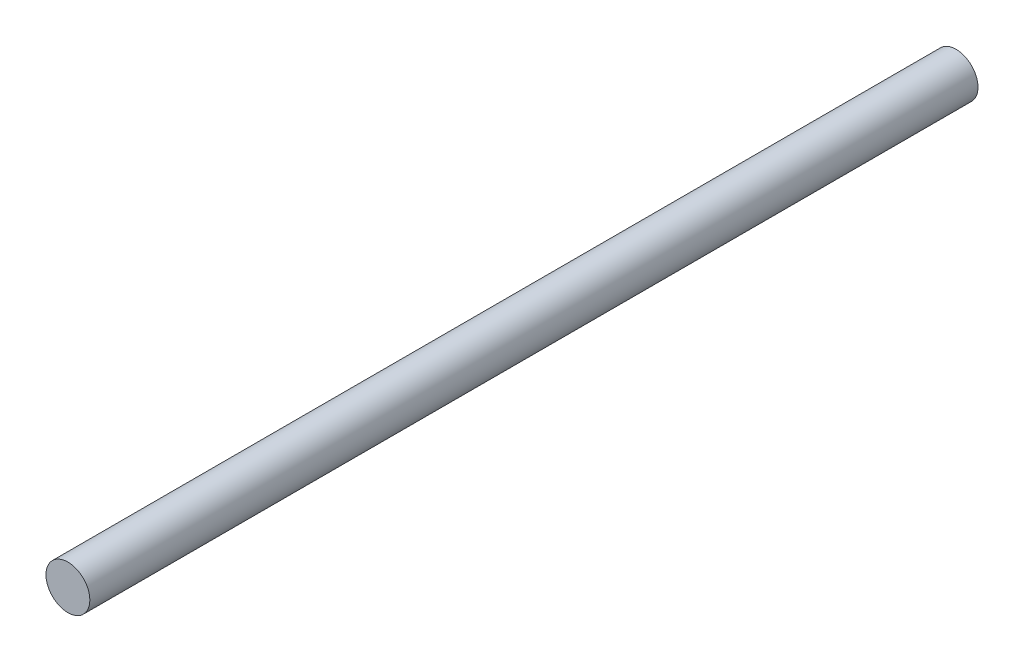
SolidWorks part; units mm, degrees
ref_plane "Front Plane" through (0, 0, 0) normal (0, 0, 1) x (1, 0, 0)
ref_plane "Top Plane" through (0, 0, 0) normal (0, 1, 0) x (1, 0, 0)
ref_plane "Right Plane" through (0, 0, 0) normal (1, 0, 0) x (0, 0, -1)
sketch "Sketch1" plane through (0, 0, 0) normal (0, 0, 1) x (1, 0, 0)
  circle A0 centre (0, 0) radius 11.1125
  dimension "D1" = 22.225
extrude "Boss-Extrude1" add sketch "Sketch1" along normal blind 450
